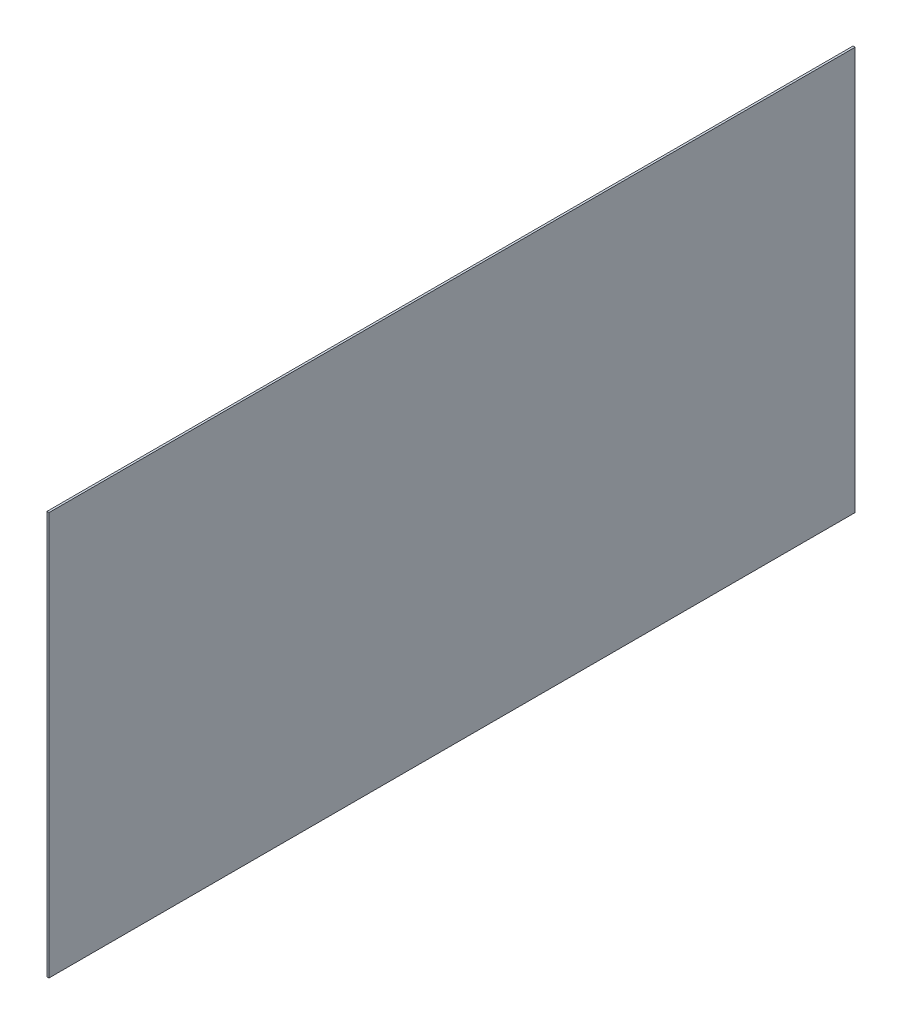
SolidWorks part; units mm, degrees
material "3003 Alloy"
ref_plane "Front Plane" through (0, 0, 0) normal (0, 0, 1) x (1, 0, 0)
ref_plane "Top Plane" through (0, 0, 0) normal (0, 1, 0) x (1, 0, 0)
ref_plane "Right Plane" through (0, 0, 0) normal (1, 0, 0) x (0, 0, -1)
sketch "Sketch1" plane through (0, 0, 0) normal (1, 0, 0) x (0, 0, -1)
  line L1 (0, 0) -> (1828.8, 0)
  line L2 (0, 0) -> (0, 914.4)
  line L3 (0, 914.4) -> (1828.8, 914.4)
  line L4 (1828.8, 0) -> (1828.8, 914.4)
  dimension "D1" = 914.4
  dimension "D2" = 1828.8
extrude "Boss-Extrude1" add sketch "Sketch1" along normal blind 4.7625
